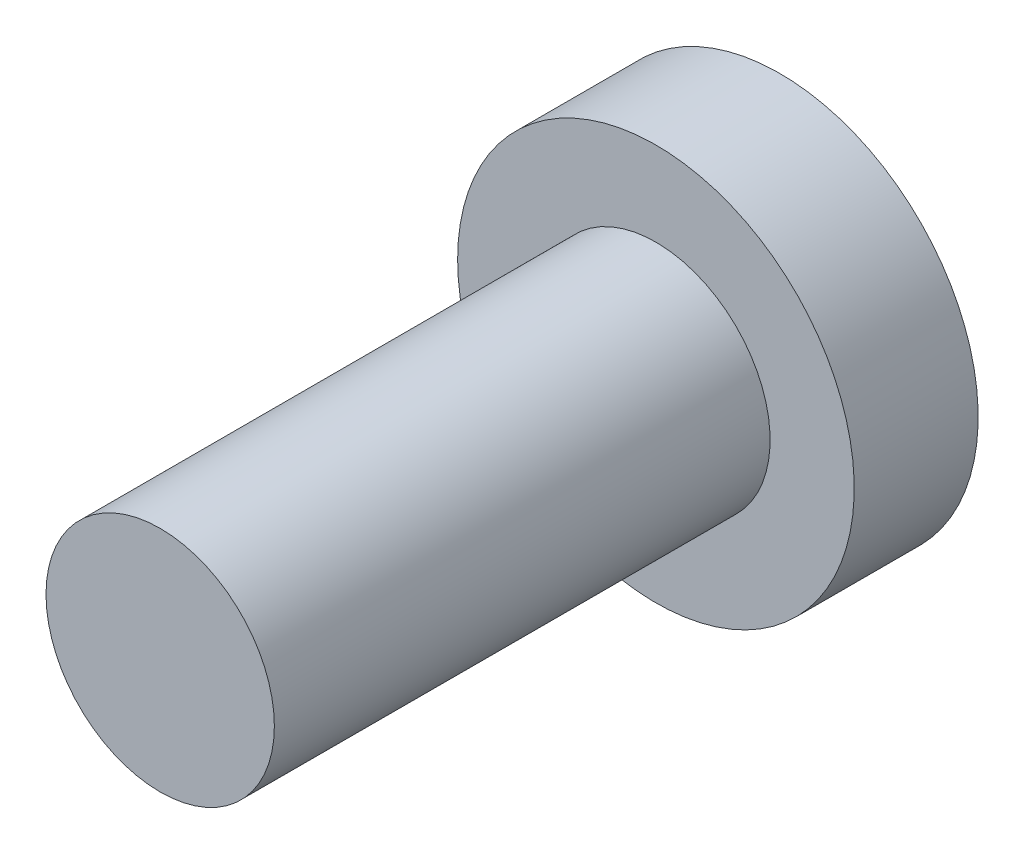
SolidWorks part; units mm, degrees
ref_plane "Front Plane" through (0, 0, 0) normal (0, 0, 1) x (1, 0, 0)
ref_plane "Top Plane" through (0, 0, 0) normal (0, 1, 0) x (1, 0, 0)
ref_plane "Right Plane" through (0, 0, 0) normal (1, 0, 0) x (0, 0, -1)
sketch "Sketch1" plane through (0, 0, 0) normal (0, 0, 1) x (1, 0, 0)
  circle A0 centre (0, 0) radius 3.175
  dimension "D1" = 6.35
extrude "Boss-Extrude1" add sketch "Sketch1" along normal blind 12.7 contours A0
sketch "Sketch2" plane through (0, 0, 0) normal (0, 0, -1) x (-1, 0, 0)
  circle A0 centre (0, 0) radius 5.08
  dimension "D1" = 10.16
extrude "Boss-Extrude2" add sketch "Sketch2" along normal blind 3.175
other "Move Face1" face at (3.175, 0, 12.7) parameters "D1"=0.25
